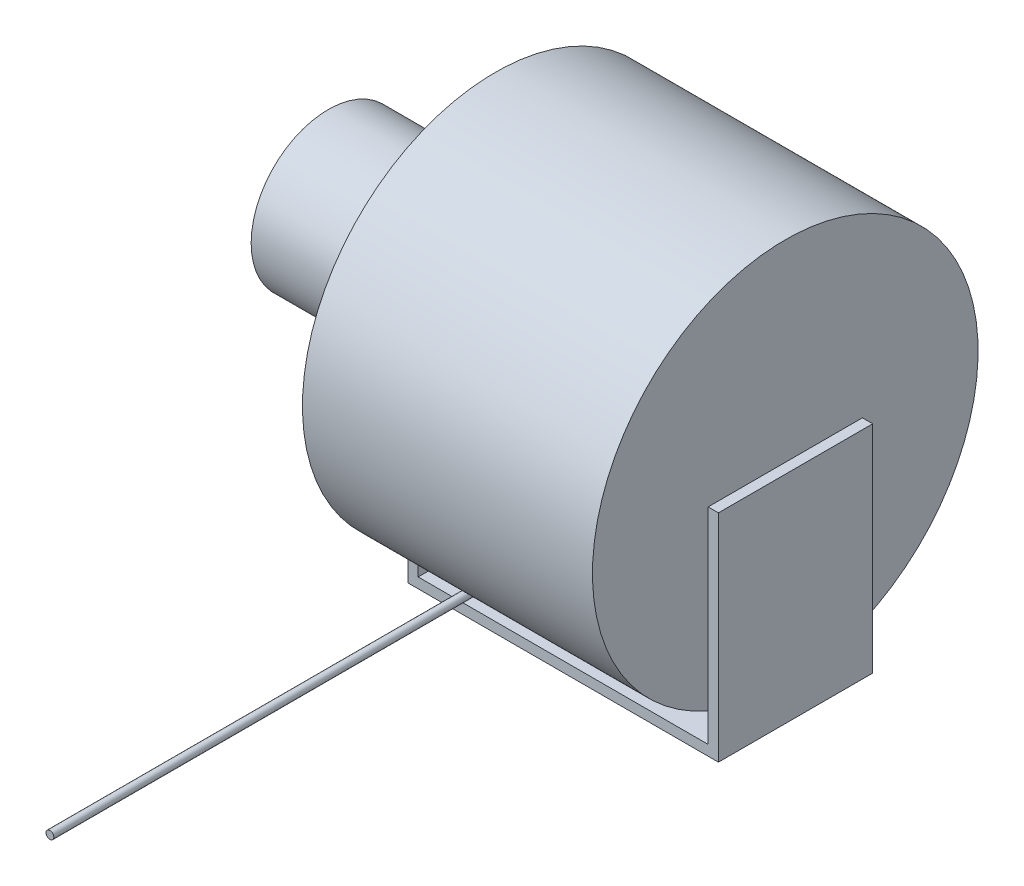
SolidWorks part; units mm, degrees
ref_plane "Front Plane" through (0, 0, 0) normal (0, 0, 1) x (1, 0, 0)
ref_plane "Top Plane" through (0, 0, 0) normal (0, 1, 0) x (1, 0, 0)
ref_plane "Right Plane" through (0, 0, 0) normal (1, 0, 0) x (0, 0, -1)
sketch "Sketch1" plane through (0, 0, 0) normal (1, 0, 0) x (0, 0, -1)
  circle A0 centre (0, 0) radius 187.5
  dimension "D1" = 375
extrude "Boss-Extrude1" add sketch "Sketch1" along normal blind 282
sketch "Sketch2" plane through (0, 0, 0) normal (-1, 0, 0) x (0, 0, 1)
  line L0 (-75, 0) -> (75, 0)
  line L1 (-75, 0) -> (-75, -210)
  line L2 (75, 0) -> (75, -210)
  line L3 (-75, -210) -> (75, -210)
  dimension "D1" = 150
  dimension "D2" = 75
  dimension "D3" = 210
extrude "Boss-Extrude2" add sketch "Sketch2" along normal blind 10
sketch "Sketch3" plane through (282, 0, 0) normal (1, 0, 0) x (0, 0, -1)
  line L0 (-75, 0) -> (75, 0)
  line L1 (-75, 0) -> (-75, -210)
  line L2 (75, 0) -> (75, -210)
  line L3 (-75, -210) -> (75, -210)
  dimension "D1" = 75
  dimension "D2" = 150
  dimension "D3" = 210
extrude "Boss-Extrude3" add sketch "Sketch3" along normal blind 10
sketch "Sketch4" plane through (0, 0, 0) normal (1, 0, 0) x (0, 0, -1)
  line L0 (75, -210) -> (-75, -210)
  line L1 (75, -210) -> (75, -200)
  line L2 (-75, -210) -> (-75, -200)
  line L3 (75, -200) -> (-75, -200)
  dimension "D1" = 10
extrude "Boss-Extrude4" add sketch "Sketch4" along normal up to next
sketch "Sketch5" plane through (-10, 0, 0) normal (-1, 0, 0) x (0, 0, 1)
  line L0 (75, 0) -> (-75, 0) construction
  circle A0 centre (0, 0) radius 75
  dimension "D1" = 150
extrude "Boss-Extrude5" add sketch "Sketch5" along normal blind 152.4
ref_plane "Plane1" through (50.7, 0, 0) normal (1, 0, 0) x (0, 0, -1)
sketch "Sketch6" plane through (50.7, 0, 0) normal (1, 0, 0) x (0, 0, -1)
  line L0 (0, -187.5) -> (0, 0) construction
  line L1 (0, -187.5) -> (-200, -187.5)
  dimension "D1" = 200
ref_plane "Plane3" through (0, 0, 200) normal (0, 0, 1) x (1, 0, 0)
sketch "Sketch8" plane through (0, 0, 200) normal (0, 0, 1) x (1, 0, 0)
  circle A0 centre (50.7, -187.5) radius 3.8
  dimension "D1" = 7.6
sweep "Sweep2" add profiles "Sketch8" path "Sketch6"
sketch "Sketch9" plane through (0, 0, 200) normal (0, 0, 1) x (1, 0, 0)
  circle A0 centre (50.7, -187.5) radius 3.8
extrude "Boss-Extrude6" add sketch "Sketch9" along normal blind 283.8
